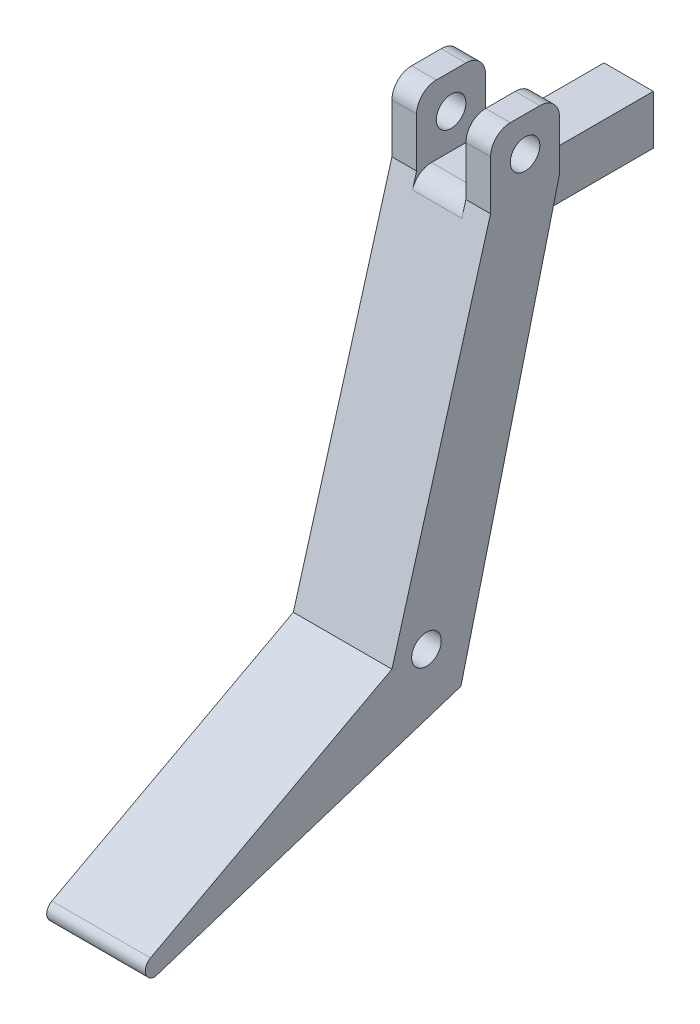
SolidWorks part; units mm, degrees
ref_plane "Front Plane" through (0, 0, 0) normal (0, 0, 1) x (1, 0, 0)
ref_plane "Top Plane" through (0, 0, 0) normal (0, 1, 0) x (1, 0, 0)
ref_plane "Right Plane" through (0, 0, 0) normal (1, 0, 0) x (0, 0, -1)
sketch "Sketch1" plane through (0, 0, 0) normal (1, 0, 0) x (0, 0, -1)
  line L0 (-37.8235, -17.2941) -> (-22.8235, -17.2941)
  line L1 (-22.8235, -17.2941) -> (-2.8235, -7.2941)
  line L2 (-2.8235, -7.2941) -> (7.1765, 32.7059)
  line L3 (7.1765, 32.7059) -> (7.1765, 39.7059)
  line L4 (7.1765, 39.7059) -> (0.1765, 39.7059)
  line L5 (0.1765, 39.7059) -> (0.1765, 32.7059)
  line L6 (0.1765, 32.7059) -> (-9.8235, -2.2941)
  line L7 (-9.8235, -2.2941) -> (-37.8235, -17.2941)
  circle A0 centre (3.6765, 36.2059) radius 1.5
  circle A1 centre (-6.3235, -2.2941) radius 1.5
  dimension "D11" = 3.5
  dimension "D13" = 3.5
  dimension "D1" = 7
  dimension "D2" = 7
  dimension "D3" = 7
  dimension "D4" = 35
  dimension "40ü" = 40
  dimension "D5" = 10
  dimension "D6" = 20
  dimension "D7" = 15
  dimension "D8" = 15
  dimension "D9" = 10
  dimension "D10" = 10
  dimension "D12" = 3.5
extrude "Boss-Extrude1" add sketch "Sketch1" along normal blind 10
fillet "Fillet1" radius 1 1 edges at (5, -17.2941, 37.8235)
sketch "Sketch2" plane through (0, 39.7059, 0) normal (0, 1, 0) x (1, 0, 0)
  line L0 (10, 0.1765) -> (0, 0.1765) construction
  line L1 (7.5, 0.1765) -> (2.5, 0.1765)
  line L2 (7.5, 0.1765) -> (7.5, 7.1765)
  line L3 (7.5, 7.1765) -> (2.5, 7.1765)
  line L4 (2.5, 0.1765) -> (2.5, 7.1765)
  line L5 (10, 7.1765) -> (0, 7.1765) construction
  dimension "D1" = 5
  dimension "D2" = 2.5
extrude "Cut-Extrude1" cut sketch "Sketch2" against normal blind 7
fillet "Fillet3" radius 2 5 edges at (5, 32.7059, -0.1765) (8.75, 39.7059, -0.1765) (8.75, 39.7059, -7.1765) (1.25, 39.7059, -7.1765) (1.25, 39.7059, -0.1765)
sketch "Sketch3" plane through (10, 0, 0) normal (1, 0, 0) x (0, 0, -1)
  line L0 (-33.8392, -17.2941) -> (-2.8235, -7.2941)
  line L1 (-2.8235, -7.2941) -> (-22.8235, -17.2941)
  line L2 (-22.8235, -17.2941) -> (-33.8392, -17.2941)
extrude "Cut-Extrude2" cut sketch "Sketch3" against normal blind 20
sketch "Sketch4" plane through (0, 32.7059, 0) normal (0, 1, 0) x (1, 0, 0)
  line L1 (2.5, 1.6851) -> (7.5, 1.6851)
  line L2 (2.5, 1.6851) -> (2.5, 19.1851)
  line L3 (2.5, 19.1851) -> (7.5, 19.1851)
  line L4 (7.5, 1.6851) -> (7.5, 19.1851)
  dimension "D1" = 5
  dimension "D2" = 17.5
extrude "Boss-Extrude3" add sketch "Sketch4" against normal blind 5
